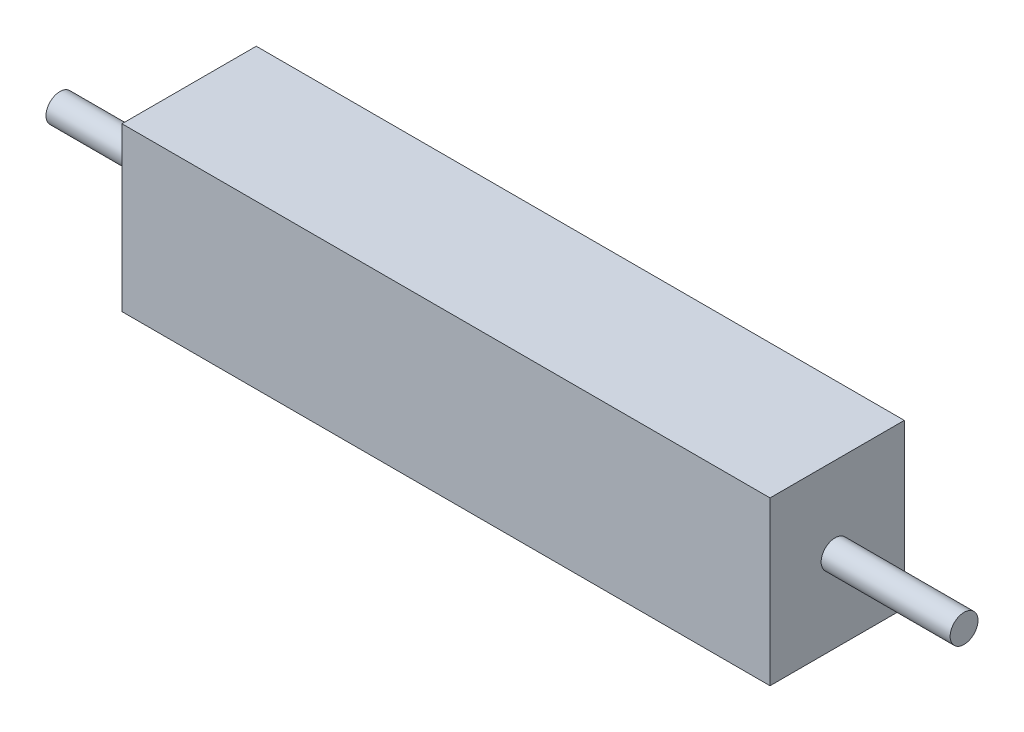
SolidWorks part; units mm, degrees
ref_plane "Front Plane" through (0, 0, 0) normal (0, 0, 1) x (1, 0, 0)
ref_plane "Top Plane" through (0, 0, 0) normal (0, 1, 0) x (1, 0, 0)
ref_plane "Right Plane" through (0, 0, 0) normal (1, 0, 0) x (0, 0, -1)
sketch "Sketch1" plane through (0, 0, 0) normal (0, 1, 0) x (1, 0, 0)
  line L1 (0, 0) -> (11.63, 0)
  line L2 (0, 0) -> (0, 2.41)
  line L3 (0, 2.41) -> (11.63, 2.41)
  line L4 (11.63, 0) -> (11.63, 2.41)
  dimension "D1" = 11.63
  dimension "D2" = 2.41
extrude "Boss-Extrude1" add sketch "Sketch1" along normal blind 2.92
sketch "Sketch2" plane through (11.63, 0, 0) normal (1, 0, 0) x (0, 0, -1)
  circle A0 centre (1.1672, 1.4657) radius 0.25
extrude "Boss-Extrude2" add sketch "Sketch2" along normal blind 2.315
sketch "Sketch3" plane through (0, 0, 0) normal (-1, 0, 0) x (0, 0, 1)
  circle A0 centre (-1.2017, 1.4128) radius 0.25
extrude "Boss-Extrude3" add sketch "Sketch3" along normal blind 2.315
